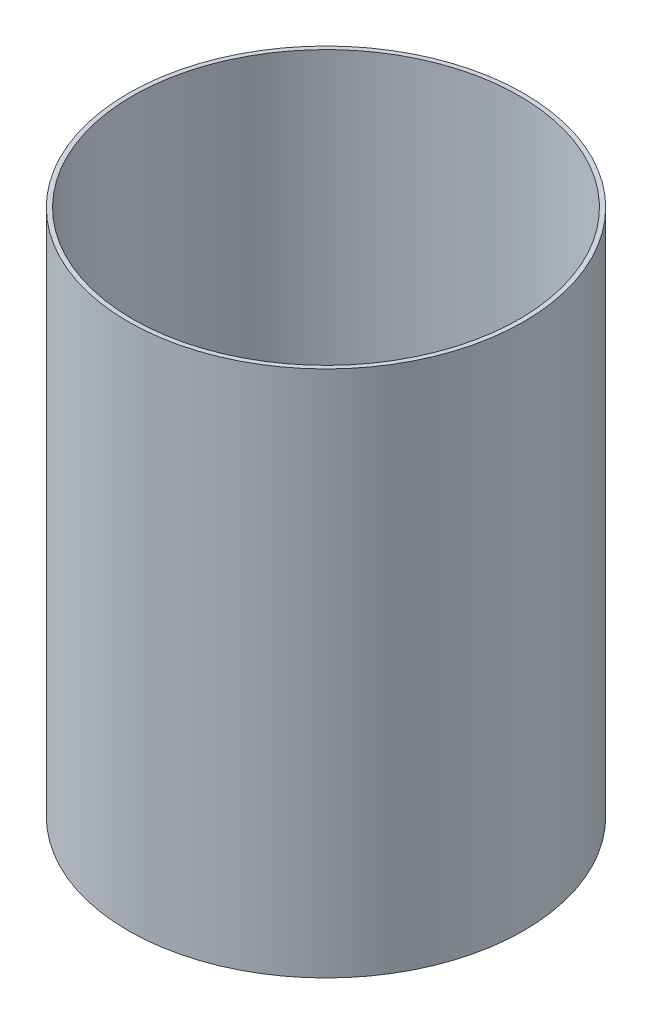
SolidWorks part; units mm, degrees
ref_plane "Front Plane" through (0, 0, 0) normal (0, 0, 1) x (1, 0, 0)
ref_plane "Top Plane" through (0, 0, 0) normal (0, 1, 0) x (1, 0, 0)
ref_plane "Right Plane" through (0, 0, 0) normal (1, 0, 0) x (0, 0, -1)
sketch "Sketch1" plane through (0, 0, 0) normal (0, 1, 0) x (1, 0, 0)
  circle A0 centre (0, 0) radius 225
  dimension "D1" = 450
extrude "Boss-Extrude1" add sketch "Sketch1" along normal blind 600
shell "Shell1" thickness 5
